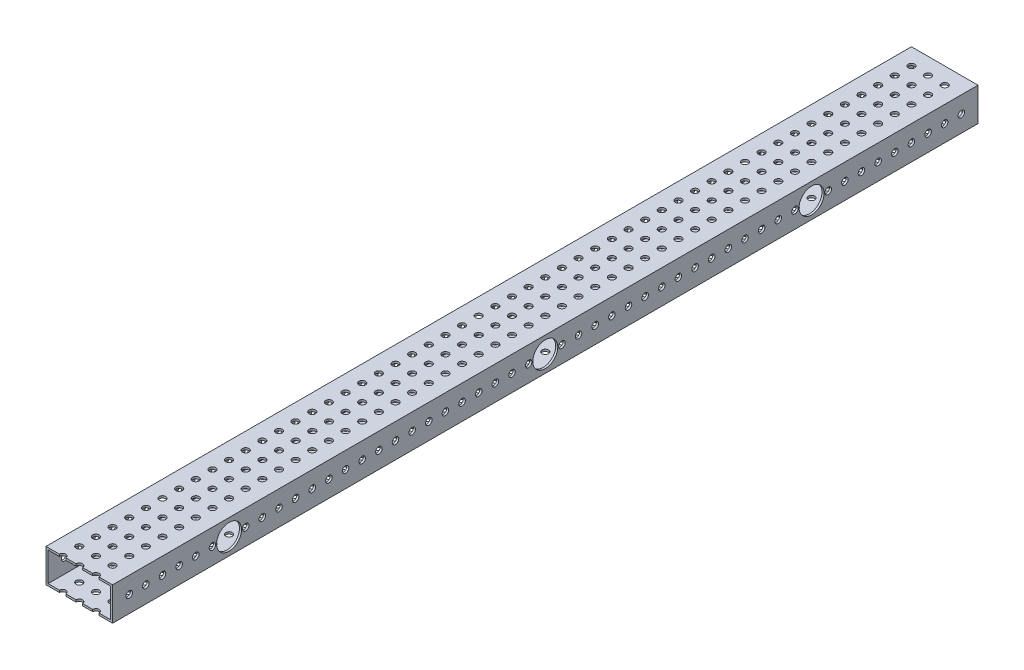
SolidWorks part; units mm, degrees
material "6061 Alloy"
ref_plane "Front Plane" through (0, 0, 0) normal (0, 0, 1) x (1, 0, 0)
ref_plane "Top Plane" through (0, 0, 0) normal (0, 1, 0) x (1, 0, 0)
ref_plane "Right Plane" through (0, 0, 0) normal (1, 0, 0) x (0, 0, -1)
sketch "Sketch1" plane through (0, 0, 0) normal (0, 0, 1) x (1, 0, 0)
  line L1 (0, 0) -> (50.8, 0)
  line L2 (0, 0) -> (0, 25.4)
  line L3 (0, 25.4) -> (50.8, 25.4)
  line L4 (50.8, 0) -> (50.8, 25.4)
  dimension "D1" = 25.4
  dimension "D2" = 50.8
extrude "Boss-Extrude1" add sketch "Sketch1" along normal blind 660.4
sketch "Sketch2" plane through (0, 0, 660.4) normal (0, 0, 1) x (1, 0, 0)
  line L14 (49.2125, 1.5875) -> (49.2125, 23.8125)
  line L15 (1.5875, 1.5875) -> (49.2125, 1.5875)
  line L16 (1.5875, 23.8125) -> (1.5875, 1.5875)
  line L17 (49.2125, 23.8125) -> (1.5875, 23.8125)
  line L18 (49.2125, 1.5875) -> (49.2125, 23.8125)
  line L19 (1.5875, 1.5875) -> (49.2125, 1.5875)
  line L20 (1.5875, 23.8125) -> (1.5875, 1.5875)
  line L21 (49.2125, 23.8125) -> (1.5875, 23.8125)
  dimension "D1" = 1.5875
extrude "Cut-Extrude1" cut sketch "Sketch2" against normal through all
sketch "Sketch3" plane through (50.8, 0, 0) normal (1, 0, 0) x (0, 0, -1)
  line L0 (-660.4, 0) -> (-660.4, 25.4) construction
  line L1 (-647.7, 12.7) -> (-635, 12.7) construction
  circle A0 centre (-647.7, 12.7) radius 2.4892
  circle A1 centre (-635, 12.7) radius 2.4892
  circle A2 centre (-622.3, 12.7) radius 2.4892
  circle A3 centre (-609.6, 12.7) radius 2.4892
  circle A4 centre (-596.9, 12.7) radius 2.4892
  circle A5 centre (-584.2, 12.7) radius 2.4892
  circle A6 centre (-571.5, 12.7) radius 2.4892
  circle A7 centre (-558.8, 12.7) radius 2.4892
  circle A8 centre (-546.1, 12.7) radius 2.4892
  circle A9 centre (-533.4, 12.7) radius 2.4892
  circle A10 centre (-520.7, 12.7) radius 2.4892
  circle A11 centre (-508, 12.7) radius 2.4892
  circle A12 centre (-495.3, 12.7) radius 2.4892
  circle A13 centre (-482.6, 12.7) radius 2.4892
  circle A14 centre (-469.9, 12.7) radius 2.4892
  circle A15 centre (-457.2, 12.7) radius 2.4892
  circle A16 centre (-444.5, 12.7) radius 2.4892
  circle A17 centre (-431.8, 12.7) radius 2.4892
  circle A18 centre (-419.1, 12.7) radius 2.4892
  circle A19 centre (-406.4, 12.7) radius 2.4892
  circle A20 centre (-393.7, 12.7) radius 2.4892
  circle A21 centre (-381, 12.7) radius 2.4892
  circle A22 centre (-368.3, 12.7) radius 2.4892
  circle A23 centre (-355.6, 12.7) radius 2.4892
  circle A24 centre (-342.9, 12.7) radius 2.4892
  circle A25 centre (-330.2, 12.7) radius 2.4892
  circle A26 centre (-317.5, 12.7) radius 2.4892
  circle A27 centre (-304.8, 12.7) radius 2.4892
  circle A28 centre (-292.1, 12.7) radius 2.4892
  circle A29 centre (-279.4, 12.7) radius 2.4892
  circle A30 centre (-266.7, 12.7) radius 2.4892
  circle A31 centre (-254, 12.7) radius 2.4892
  circle A32 centre (-241.3, 12.7) radius 2.4892
  circle A33 centre (-228.6, 12.7) radius 2.4892
  circle A34 centre (-215.9, 12.7) radius 2.4892
  circle A35 centre (-203.2, 12.7) radius 2.4892
  circle A36 centre (-190.5, 12.7) radius 2.4892
  circle A37 centre (-177.8, 12.7) radius 2.4892
  circle A38 centre (-165.1, 12.7) radius 2.4892
  circle A39 centre (-152.4, 12.7) radius 2.4892
  circle A40 centre (-139.7, 12.7) radius 2.4892
  circle A41 centre (-127, 12.7) radius 2.4892
  circle A42 centre (-114.3, 12.7) radius 2.4892
  circle A43 centre (-101.6, 12.7) radius 2.4892
  circle A44 centre (-88.9, 12.7) radius 2.4892
  circle A45 centre (-76.2, 12.7) radius 2.4892
  circle A46 centre (-63.5, 12.7) radius 2.4892
  circle A47 centre (-50.8, 12.7) radius 2.4892
  circle A48 centre (-38.1, 12.7) radius 2.4892
  circle A49 centre (-25.4, 12.7) radius 2.4892
  circle A50 centre (-12.7, 12.7) radius 2.4892
  point P5 (-660.4, 12.7)
  dimension "D1" = 4.9784
  dimension "D2" = 12.7
  dimension "D4" = 12.7
  dimension "D3" = 51
extrude "Cut-Extrude2" cut sketch "Sketch3" along direction (-1, 0, 0) on the side against the normal through all
sketch "Sketch4" plane through (0, 25.4, 0) normal (0, 1, 0) x (1, 0, 0)
  line L0 (0, -88.9) -> (50.8, -88.9) construction
  line L1 (0, -660.4) -> (0, 0) construction
  line L2 (50.8, -660.4) -> (50.8, 0) construction
  line L3 (0, -495.3) -> (50.8, -495.3) construction
  line L4 (50.8, 0) -> (0, 0) construction
  line L5 (0, -114.3) -> (50.8, -114.3) construction
  line L6 (0, -469.9) -> (50.8, -469.9) construction
  line L7 (0, -101.6) -> (50.8, -101.6) construction
  line L8 (12.7, -101.6) -> (25.4, -101.6) construction
  line L9 (25.4, -88.9) -> (25.4, -114.3) construction
  line L10 (50.8, -330.2) -> (0, -330.2) construction
  circle A0 centre (12.7, -101.6) radius 2.4892
  circle A1 centre (25.4, -101.6) radius 2.4892
  circle A2 centre (38.1, -101.6) radius 2.4892
  circle A3 centre (38.1, -558.8) radius 2.4892
  circle A4 centre (25.4, -558.8) radius 2.4892
  circle A5 centre (12.7, -558.8) radius 2.4892
  point P14 (25.4, -88.9)
  point P15 (25.4, -495.3)
  dimension "D5" = 4.9784
  dimension "D1" = 406.4
  dimension "D2" = 88.9
  dimension "D3" = 25.4
  dimension "D4" = 25.4
  dimension "D7" = 12.7
  dimension "D6" = 3
extrude "Cut-Extrude3" cut sketch "Sketch4" against normal up to next and the other way through all
sketch "Sketch6" plane through (50.8, 0, 0) normal (1, 0, 0) x (0, 0, -1)
  line L1 (-660.4, 0) -> (0, 0) construction
  line L2 (-330.2, 25.4) -> (-330.2, 0) construction
  line L3 (-660.4, 25.4) -> (0, 25.4) construction
  circle A0 centre (-571.5, 12.7) radius 9.525
  circle A1 centre (-127, 12.7) radius 9.525
  circle A2 centre (-330.2, 12.7) radius 9.525
  circle A5 centre (-558.8, 12.7) radius 2.4892 construction
  dimension "D1" = 19.05
  dimension "D2" = 19.05
  dimension "D5" = 19.05
  dimension "D3" = 12.7
  dimension "D4" = 12.7
extrude "Cut-Extrude5" cut sketch "Sketch6" against normal through all
sketch "Sketch8" plane through (0, 25.4, 0) normal (0, 1, 0) x (1, 0, 0)
  line L0 (0, -660.4) -> (0, 0) construction
  line L1 (50.8, 0) -> (0, 0) construction
  line L2 (12.7, -12.7) -> (25.4, -12.7) construction
  line L3 (12.7, -12.7) -> (12.7, -25.4) construction
  circle A0 centre (12.7, -12.7) radius 2.4892
  circle A1 centre (25.4, -12.7) radius 2.4892
  circle A2 centre (38.1, -12.7) radius 2.4892
  circle A3 centre (25.4, -25.4) radius 2.4892
  circle A4 centre (38.1, -25.4) radius 2.4892
  circle A5 centre (25.4, -38.1) radius 2.4892
  circle A6 centre (38.1, -38.1) radius 2.4892
  circle A7 centre (25.4, -50.8) radius 2.4892
  circle A8 centre (38.1, -50.8) radius 2.4892
  circle A9 centre (25.4, -63.5) radius 2.4892
  circle A10 centre (38.1, -63.5) radius 2.4892
  circle A11 centre (25.4, -76.2) radius 2.4892
  circle A12 centre (38.1, -76.2) radius 2.4892
  circle A13 centre (25.4, -88.9) radius 2.4892
  circle A14 centre (38.1, -88.9) radius 2.4892
  circle A15 centre (25.4, -101.6) radius 2.4892
  circle A16 centre (38.1, -101.6) radius 2.4892
  circle A17 centre (25.4, -114.3) radius 2.4892
  circle A18 centre (38.1, -114.3) radius 2.4892
  circle A19 centre (25.4, -127) radius 2.4892
  circle A20 centre (38.1, -127) radius 2.4892
  circle A21 centre (25.4, -139.7) radius 2.4892
  circle A22 centre (38.1, -139.7) radius 2.4892
  circle A23 centre (25.4, -152.4) radius 2.4892
  circle A24 centre (38.1, -152.4) radius 2.4892
  circle A25 centre (25.4, -165.1) radius 2.4892
  circle A26 centre (38.1, -165.1) radius 2.4892
  circle A27 centre (25.4, -177.8) radius 2.4892
  circle A28 centre (38.1, -177.8) radius 2.4892
  circle A29 centre (25.4, -190.5) radius 2.4892
  circle A30 centre (38.1, -190.5) radius 2.4892
  circle A31 centre (25.4, -203.2) radius 2.4892
  circle A32 centre (38.1, -203.2) radius 2.4892
  circle A33 centre (25.4, -215.9) radius 2.4892
  circle A34 centre (38.1, -215.9) radius 2.4892
  circle A35 centre (25.4, -228.6) radius 2.4892
  circle A36 centre (38.1, -228.6) radius 2.4892
  circle A37 centre (25.4, -241.3) radius 2.4892
  circle A38 centre (38.1, -241.3) radius 2.4892
  circle A39 centre (25.4, -254) radius 2.4892
  circle A40 centre (38.1, -254) radius 2.4892
  circle A41 centre (25.4, -266.7) radius 2.4892
  circle A42 centre (38.1, -266.7) radius 2.4892
  circle A43 centre (25.4, -279.4) radius 2.4892
  circle A44 centre (38.1, -279.4) radius 2.4892
  circle A45 centre (25.4, -292.1) radius 2.4892
  circle A46 centre (38.1, -292.1) radius 2.4892
  circle A47 centre (25.4, -304.8) radius 2.4892
  circle A48 centre (38.1, -304.8) radius 2.4892
  circle A49 centre (25.4, -317.5) radius 2.4892
  circle A50 centre (38.1, -317.5) radius 2.4892
  circle A51 centre (25.4, -330.2) radius 2.4892
  circle A52 centre (38.1, -330.2) radius 2.4892
  circle A53 centre (25.4, -342.9) radius 2.4892
  circle A54 centre (38.1, -342.9) radius 2.4892
  circle A55 centre (25.4, -355.6) radius 2.4892
  circle A56 centre (38.1, -355.6) radius 2.4892
  circle A57 centre (25.4, -368.3) radius 2.4892
  circle A58 centre (38.1, -368.3) radius 2.4892
  circle A59 centre (25.4, -381) radius 2.4892
  circle A60 centre (38.1, -381) radius 2.4892
  circle A61 centre (25.4, -393.7) radius 2.4892
  circle A62 centre (38.1, -393.7) radius 2.4892
  circle A63 centre (25.4, -406.4) radius 2.4892
  circle A64 centre (38.1, -406.4) radius 2.4892
  circle A65 centre (25.4, -419.1) radius 2.4892
  circle A66 centre (38.1, -419.1) radius 2.4892
  circle A67 centre (25.4, -431.8) radius 2.4892
  circle A68 centre (38.1, -431.8) radius 2.4892
  circle A69 centre (25.4, -444.5) radius 2.4892
  circle A70 centre (38.1, -444.5) radius 2.4892
  circle A71 centre (25.4, -457.2) radius 2.4892
  circle A72 centre (38.1, -457.2) radius 2.4892
  circle A73 centre (25.4, -469.9) radius 2.4892
  circle A74 centre (38.1, -469.9) radius 2.4892
  circle A75 centre (25.4, -482.6) radius 2.4892
  circle A76 centre (38.1, -482.6) radius 2.4892
  circle A77 centre (25.4, -495.3) radius 2.4892
  circle A78 centre (38.1, -495.3) radius 2.4892
  circle A79 centre (25.4, -508) radius 2.4892
  circle A80 centre (38.1, -508) radius 2.4892
  circle A81 centre (25.4, -520.7) radius 2.4892
  circle A82 centre (38.1, -520.7) radius 2.4892
  circle A83 centre (25.4, -533.4) radius 2.4892
  circle A84 centre (38.1, -533.4) radius 2.4892
  circle A85 centre (25.4, -546.1) radius 2.4892
  circle A86 centre (38.1, -546.1) radius 2.4892
  circle A87 centre (25.4, -558.8) radius 2.4892
  circle A88 centre (38.1, -558.8) radius 2.4892
  circle A89 centre (25.4, -571.5) radius 2.4892
  circle A90 centre (38.1, -571.5) radius 2.4892
  circle A91 centre (25.4, -584.2) radius 2.4892
  circle A92 centre (38.1, -584.2) radius 2.4892
  circle A93 centre (25.4, -596.9) radius 2.4892
  circle A94 centre (38.1, -596.9) radius 2.4892
  circle A95 centre (25.4, -609.6) radius 2.4892
  circle A96 centre (38.1, -609.6) radius 2.4892
  circle A97 centre (25.4, -622.3) radius 2.4892
  circle A98 centre (38.1, -622.3) radius 2.4892
  circle A99 centre (25.4, -635) radius 2.4892
  circle A100 centre (38.1, -635) radius 2.4892
  circle A101 centre (25.4, -647.7) radius 2.4892
  circle A102 centre (38.1, -647.7) radius 2.4892
  circle A103 centre (25.4, -660.4) radius 2.4892
  circle A104 centre (38.1, -660.4) radius 2.4892
  circle A105 centre (12.7, -25.4) radius 2.4892
  circle A106 centre (12.7, -38.1) radius 2.4892
  circle A107 centre (12.7, -50.8) radius 2.4892
  circle A108 centre (12.7, -63.5) radius 2.4892
  circle A109 centre (12.7, -76.2) radius 2.4892
  circle A110 centre (12.7, -88.9) radius 2.4892
  circle A111 centre (12.7, -101.6) radius 2.4892
  circle A112 centre (12.7, -114.3) radius 2.4892
  circle A113 centre (12.7, -127) radius 2.4892
  circle A114 centre (12.7, -139.7) radius 2.4892
  circle A115 centre (12.7, -152.4) radius 2.4892
  circle A116 centre (12.7, -165.1) radius 2.4892
  circle A117 centre (12.7, -177.8) radius 2.4892
  circle A118 centre (12.7, -190.5) radius 2.4892
  circle A119 centre (12.7, -203.2) radius 2.4892
  circle A120 centre (12.7, -215.9) radius 2.4892
  circle A121 centre (12.7, -228.6) radius 2.4892
  circle A122 centre (12.7, -241.3) radius 2.4892
  circle A123 centre (12.7, -254) radius 2.4892
  circle A124 centre (12.7, -266.7) radius 2.4892
  circle A125 centre (12.7, -279.4) radius 2.4892
  circle A126 centre (12.7, -292.1) radius 2.4892
  circle A127 centre (12.7, -304.8) radius 2.4892
  circle A128 centre (12.7, -317.5) radius 2.4892
  circle A129 centre (12.7, -330.2) radius 2.4892
  circle A130 centre (12.7, -342.9) radius 2.4892
  circle A131 centre (12.7, -355.6) radius 2.4892
  circle A132 centre (12.7, -368.3) radius 2.4892
  circle A133 centre (12.7, -381) radius 2.4892
  circle A134 centre (12.7, -393.7) radius 2.4892
  circle A135 centre (12.7, -406.4) radius 2.4892
  circle A136 centre (12.7, -419.1) radius 2.4892
  circle A137 centre (12.7, -431.8) radius 2.4892
  circle A138 centre (12.7, -444.5) radius 2.4892
  circle A139 centre (12.7, -457.2) radius 2.4892
  circle A140 centre (12.7, -469.9) radius 2.4892
  circle A141 centre (12.7, -482.6) radius 2.4892
  circle A142 centre (12.7, -495.3) radius 2.4892
  circle A143 centre (12.7, -508) radius 2.4892
  circle A144 centre (12.7, -520.7) radius 2.4892
  circle A145 centre (12.7, -533.4) radius 2.4892
  circle A146 centre (12.7, -546.1) radius 2.4892
  circle A147 centre (12.7, -558.8) radius 2.4892
  circle A148 centre (12.7, -571.5) radius 2.4892
  circle A149 centre (12.7, -584.2) radius 2.4892
  circle A150 centre (12.7, -596.9) radius 2.4892
  circle A151 centre (12.7, -609.6) radius 2.4892
  circle A152 centre (12.7, -622.3) radius 2.4892
  circle A153 centre (12.7, -635) radius 2.4892
  circle A154 centre (12.7, -647.7) radius 2.4892
  circle A155 centre (12.7, -660.4) radius 2.4892
  dimension "D1" = 4.9784
  dimension "D2" = 12.7
  dimension "D3" = 12.7
  dimension "D6" = 90
  dimension "D7" = 12.7
  dimension "D8" = 12.7
  dimension "D4" = 3
  dimension "D5" = 52
extrude "Cut-Extrude6" cut sketch "Sketch8" against normal through all
